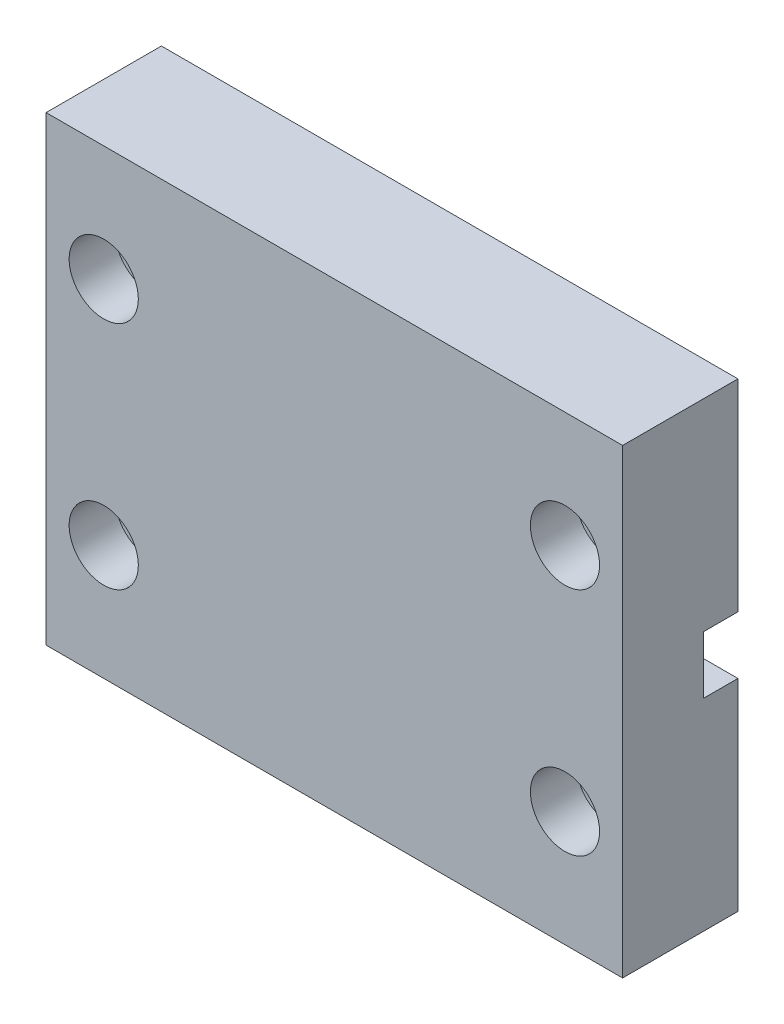
SolidWorks part; units mm, degrees
ref_plane "Front Plane" through (0, 0, 0) normal (0, 0, 1) x (1, 0, 0)
ref_plane "Top Plane" through (0, 0, 0) normal (0, 1, 0) x (1, 0, 0)
ref_plane "Right Plane" through (0, 0, 0) normal (1, 0, 0) x (0, 0, -1)
sketch "Sketch1" plane through (0, 0.8358, 0) normal (0, 1, 0) x (-1, 0, 0)
  line L1 (25.4446, 18.2898) -> (-24.5554, 18.2898)
  line L2 (25.4446, 18.2898) -> (25.4446, 28.2898)
  line L3 (25.4446, 28.2898) -> (-24.5554, 28.2898)
  line L4 (-24.5554, 18.2898) -> (-24.5554, 28.2898)
  dimension "D1" = 10
  dimension "D2" = 50
extrude "Boss-Extrude1" add sketch "Sketch1" along normal blind 40
sketch "Sketch2" plane through (0, 0, 28.2898) normal (0, 0, 1) x (1, 0, 0)
  line L0 (-25.4446, 40.8358) -> (-25.4446, 0.8358) construction
  line L1 (-25.4446, 40.8358) -> (24.5554, 40.8358) construction
  line L2 (-25.4446, 0.8358) -> (24.5554, 0.8358) construction
  line L3 (24.5554, 40.8358) -> (24.5554, 0.8358) construction
  circle A0 centre (-20.4446, 30.8358) radius 1.75
  circle A1 centre (-20.4446, 10.8358) radius 1.75
  circle A2 centre (19.5554, 10.8358) radius 1.75
  circle A3 centre (19.5554, 30.8358) radius 1.75
  dimension "D1" = 3.5
  dimension "D2" = 3.5
  dimension "D3" = 3.5
  dimension "D4" = 3.5
  dimension "D5" = 5
  dimension "D6" = 10
  dimension "D7" = 10
  dimension "D8" = 5
  dimension "D9" = 5
  dimension "D10" = 10
  dimension "D11" = 5
  dimension "D12" = 10
extrude "Cut-Extrude1" cut sketch "Sketch2" against normal up to next
sketch "Sketch3" plane through (0, 0, 28.2898) normal (0, 0, 1) x (1, 0, 0)
  circle A0 centre (-20.4446, 30.8358) radius 3
  circle A1 centre (-20.4446, 10.8358) radius 3
  circle A2 centre (19.5554, 10.8358) radius 3
  circle A3 centre (19.5554, 30.8358) radius 3
  dimension "D1" = 6
  dimension "D2" = 6
  dimension "D3" = 6
  dimension "D4" = 6
extrude "Cut-Extrude2" cut sketch "Sketch3" against normal blind 4
sketch "Sketch4" plane through (0, 0, 18.2898) normal (0, 0, -1) x (-1, 0, 0)
  line L0 (-24.5554, 20.8358) -> (25.4446, 20.8358) construction
  line L1 (-24.5554, 40.8358) -> (-24.5554, 0.8358) construction
  line L2 (25.4446, 40.8358) -> (25.4446, 0.8358) construction
  line L3 (0.4446, 40.8358) -> (0.4446, 0.8358) construction
  line L4 (-24.5554, 40.8358) -> (25.4446, 40.8358) construction
  line L5 (-24.5554, 0.8358) -> (25.4446, 0.8358) construction
  point P12 (0.4446, 20.8358)
sketch "Sketch5" plane through (0, 0, 18.2898) normal (0, 0, -1) x (-1, 0, 0)
  line L1 (0.4446, 40.8358) -> (0.4446, 0.8358) construction
  line L2 (-24.5554, 20.8358) -> (25.4446, 20.8358) construction
  circle A0 centre (5.4446, 20.8358) radius 2.5
  circle A1 centre (-4.5554, 20.8358) radius 2.5
  dimension "D1" = 5
  dimension "D2" = 5
  dimension "D3" = 0
  dimension "D4" = 5
  dimension "D5" = 0
  dimension "D6" = 5
extrude "Cut-Extrude3" cut sketch "Sketch5" against normal blind 8
sketch "Sketch6" plane through (0, 0, 18.2898) normal (0, 0, -1) x (-1, 0, 0)
  line L1 (5.4446, 23.3358) -> (25.4446, 23.3358)
  line L2 (5.4446, 23.3358) -> (5.4446, 18.3358)
  line L3 (5.4446, 18.3358) -> (25.4446, 18.3358)
  line L4 (25.4446, 23.3358) -> (25.4446, 18.3358)
  line L5 (25.4446, 40.8358) -> (25.4446, 0.8358) construction
  line L7 (-24.5554, 40.8358) -> (-24.5554, 0.8358) construction
  line L8 (-4.5554, 23.3358) -> (-24.5554, 23.3358)
  line L9 (-4.5554, 23.3358) -> (-4.5554, 18.3358)
  line L10 (-4.5554, 18.3358) -> (-24.5554, 18.3358)
  line L11 (-24.5554, 23.3358) -> (-24.5554, 18.3358)
  circle A0 centre (5.4446, 20.8358) radius 2.5 construction
  circle A1 centre (-4.5554, 20.8358) radius 2.5 construction
  dimension "D1" = 20
  dimension "D2" = 20
extrude "Cut-Extrude4" cut sketch "Sketch6" against normal blind 3
